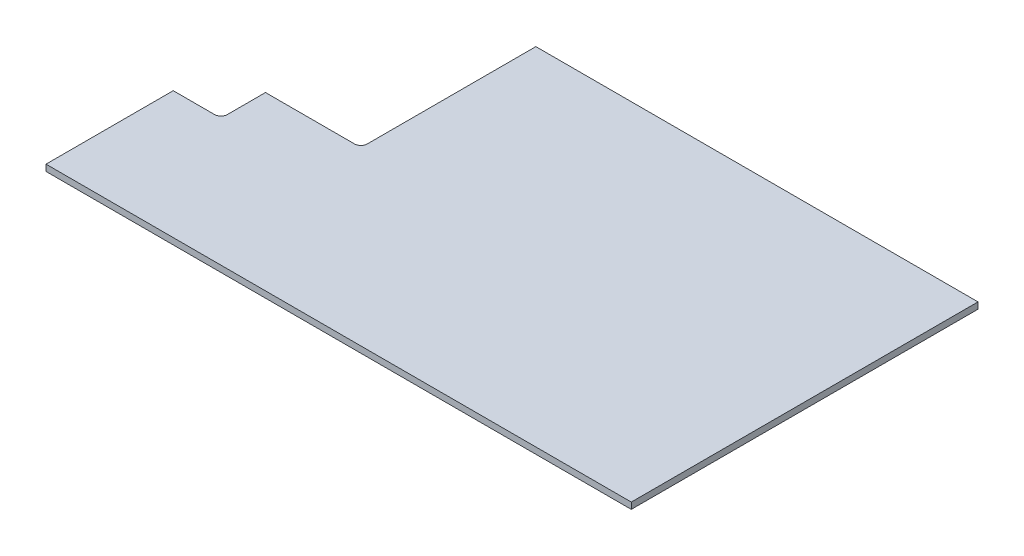
SolidWorks part; units mm, degrees
material "PTFE (general)"
ref_plane "Front" through (0, 0, 0) normal (0, 0, 1) x (1, 0, 0)
ref_plane "Top" through (0, 0, 0) normal (0, 1, 0) x (1, 0, 0)
ref_plane "Right" through (0, 0, 0) normal (1, 0, 0) x (0, 0, -1)
sketch "Sketch1" plane through (0, 0, 0) normal (0, 1, 0) x (1, 0, 0)
  line L0 (0, 0) -> (0, 27.5)
  line L1 (0, 27.5) -> (69.5, 27.5)
  line L2 (69.5, 27.5) -> (69.5, -27)
  line L3 (69.5, -27) -> (-22.5, -27)
  line L4 (-22.5, -27) -> (-22.5, -7)
  line L5 (-22.5, -7) -> (-15, -7)
  line L6 (-15, -7) -> (-15, 0)
  line L7 (-15, 0) -> (0, 0)
  dimension "D1" = 69.5
  dimension "D2" = 92
  dimension "D3" = 27.5
  dimension "D4" = 15
  dimension "D5" = 7
  dimension "D6" = 20
extrude "Boss-Extrude1" add sketch "Sketch1" along normal blind 1
fillet "Fillet1" radius 1 2 edges at (-15, 0.5, 7) (0, 0.5, 0)
